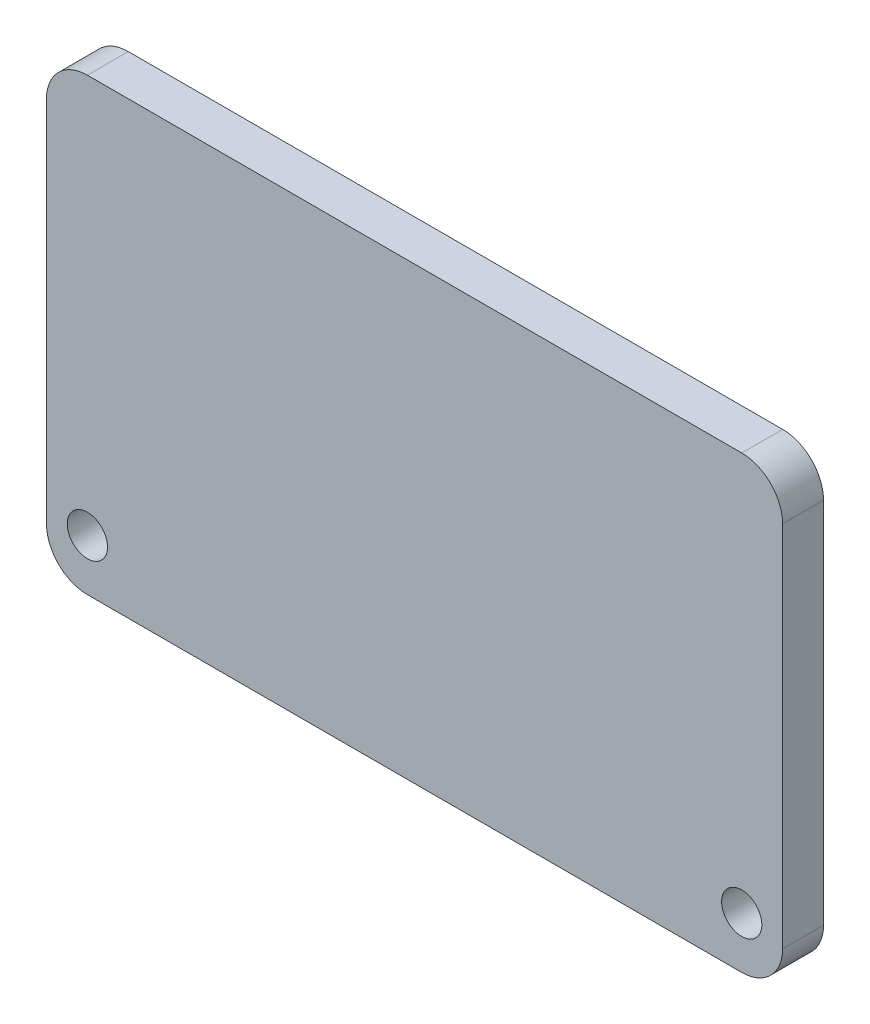
SolidWorks part; units mm, degrees
ref_plane "Front Plane" through (0, 0, 0) normal (0, 0, 1) x (1, 0, 0)
ref_plane "Top Plane" through (0, 0, 0) normal (0, 1, 0) x (1, 0, 0)
ref_plane "Right Plane" through (0, 0, 0) normal (1, 0, 0) x (0, 0, -1)
sketch "Sketch1" plane through (0, 0, 0) normal (0, 0, 1) x (1, 0, 0)
  line L1 (-22.86, -13.97) -> (22.86, -13.97)
  line L2 (-22.86, -13.97) -> (-22.86, 13.97)
  line L3 (-22.86, 13.97) -> (22.86, 13.97)
  line L4 (22.86, -13.97) -> (22.86, 13.97)
  line L5 (-22.86, -13.97) -> (22.86, 13.97) construction
  line L6 (-22.86, 13.97) -> (22.86, -13.97) construction
  point P0 (0, 0)
  dimension "D1" = 45.72
  dimension "D2" = 27.94
extrude "Boss-Extrude1" add sketch "Sketch1" along normal mid plane 2.54
fillet "Fillet1" radius 2.54 4 edges at (22.86, 13.97, 0) (22.86, -13.97, 0) (-22.86, -13.97, 0) (-22.86, 13.97, 0)
sketch "Sketch2" plane through (0, 0, 1.27) normal (0, 0, 1) x (1, 0, 0)
  line L0 (-20.32, -10.7858) -> (20.32, -10.7858) construction
  circle A0 centre (-20.32, -10.7858) radius 1.25
  circle A1 centre (20.32, -10.7858) radius 1.25
  point P4 (0, -10.7858)
  dimension "D2" = 2.5
  dimension "D1" = 40.64
extrude "Cut-Extrude1" cut sketch "Sketch2" against normal blind 2.54
